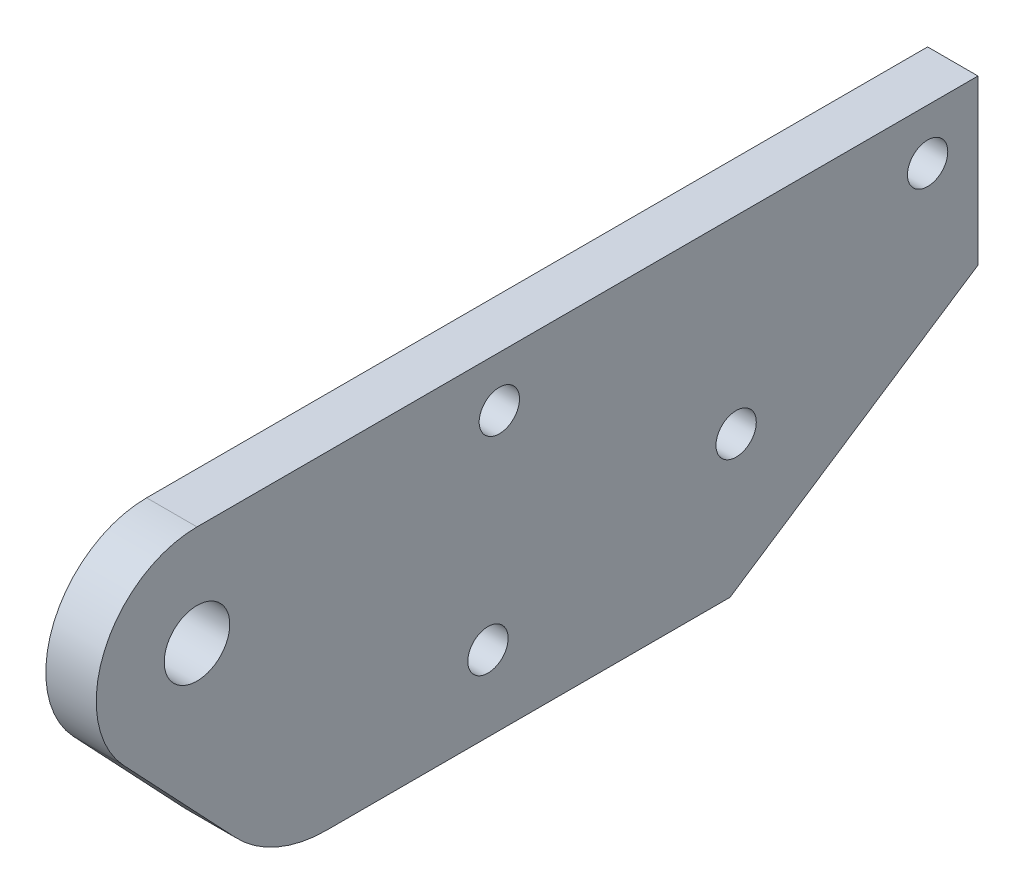
SolidWorks part; units mm, degrees
ref_plane "前视基准面" through (0, 0, 0) normal (0, 0, 1) x (1, 0, 0)
ref_plane "上视基准面" through (0, 0, 0) normal (0, 1, 0) x (1, 0, 0)
ref_plane "右视基准面" through (0, 0, 0) normal (1, 0, 0) x (0, 0, -1)
sketch "草图1" plane through (0, 0, 0) normal (1, 0, 0) x (0, 0, -1)
  line L0 (8.1049, 1.8788) -> (27.7954, 14.8788)
  line L1 (27.7954, 27.8788) -> (-34.2046, 27.8788)
  line L2 (27.7954, 27.8788) -> (27.7954, 14.8788)
  line L3 (8.1049, 1.8788) -> (-23.8951, 1.8788)
  line L10 (-31.1641, 5.0114) -> (-40.0198, 14.3849)
  circle A0 centre (23.7954, 23.8788) radius 1.6
  circle A1 centre (-10.2046, 23.8788) radius 1.6
  arc A2 (-34.2046, 27.8788) -> (-40.0198, 14.3849) centre (-34.2046, 19.8788) ccw
  circle A3 centre (8.5954, 12.8788) radius 1.6
  circle A4 centre (-11.1046, 7.8788) radius 1.6
  circle A5 centre (-34.2046, 19.8788) radius 2.6
  arc A6 (-23.8951, 1.8788) -> (-31.1641, 5.0114) centre (-23.8951, 11.8788) cw
  point P0 (-150, 0)
  point P1 (135, 0)
  point P9 (-344.9533, 138.7825)
  point P10 (187.1329, 101.1747)
  point P11 (165.9429, -19)
  point P12 (-156.9154, -19)
  dimension "D7" = 13
  dimension "D8" = 32
  dimension "D9" = 24
  dimension "D10" = 26
  dimension "D4" = 23.1
  dimension "D11" = 4
  dimension "D16" = 62
  dimension "D19" = 34
  dimension "D20" = 3.2
  dimension "D6" = 11
  dimension "D22" = 3.2
  dimension "D23" = 3.2
  dimension "D24" = 3.2
  dimension "D28" = 10
  dimension "D3" = 4
  dimension "D26" = 19.7
  dimension "D27" = 5.2
extrude "凸台-拉伸1" add sketch "草图1" along normal blind 4
